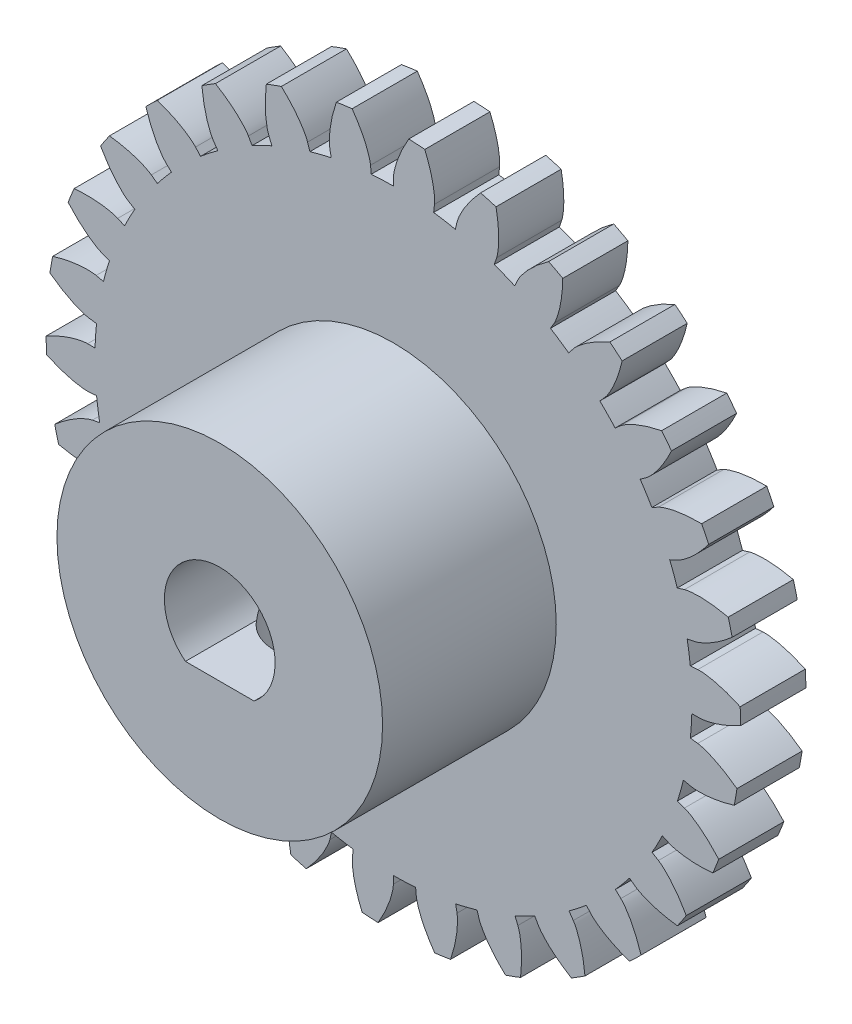
SolidWorks part; units mm, degrees
ref_plane "前视基准面" through (0, 0, 0) normal (0, 0, 1) x (1, 0, 0)
ref_plane "上视基准面" through (0, 0, 0) normal (0, 1, 0) x (1, 0, 0)
ref_plane "右视基准面" through (0, 0, 0) normal (1, 0, 0) x (0, 0, -1)
sketch "草图1" plane through (0, 0, 0) normal (0, 0, 1) x (1, 0, 0)
  line L0 (0, 14.0954) -> (-0.0077, 13.75)
  line L1 (0, 0) -> (0.2236, 14.9983) construction
  line L2 (0, 0) -> (4.2863, 18.7841) construction
  line L3 (0, 0) -> (2.4254, 20.1784) construction
  line L4 (0, 0) -> (1.3782, 20.4589) construction
  line L5 (1.8905, 13.968) -> (1.8518, 13.6247)
  line L6 (0, 0) -> (4.0005, 23.0313) construction
  line L7 (2.9306, 13.7874) -> (2.8513, 13.4511)
  circle A1 centre (0, 0) radius 16
  circle A2 centre (0, 0) radius 13.75
  circle A3 centre (0, 0) radius 15
  spline S0 degree 4 poles (0, 14.0954) (0.0003, 14.1068) (0.0017, 14.1388) (0.0077, 14.1992) (0.0217, 14.2973) (0.046, 14.4215) (0.0846, 14.5806) (0.1395, 14.766) (0.2095, 14.9673) (0.2958, 15.1832) (0.391, 15.3955) (0.4941, 15.6042) (0.6043, 15.809) (0.7462, 16.0534) (0.9281, 16.3408) (1.1575, 16.6679) (1.437, 17.028) (1.7419, 17.3821) (2.058, 17.7198) (2.3951, 18.0476) (2.7339, 18.3552) (3.1028, 18.6598) (3.4522, 18.9336) (3.8613, 19.223) (4.1968, 19.4515) (4.6573, 19.7338) (4.9346, 19.8947) (5.2648, 20.0761) (5.4146, 20.153) (5.5067, 20.2004) knots 0 0 0 0 0 0.005377 0.015084 0.028532 0.04661 0.064855 0.092111 0.119476 0.146842 0.174209 0.201575 0.228941 0.256307 0.307035 0.361767 0.4165 0.471232 0.525964 0.580697 0.635429 0.690161 0.744894 0.799626 0.854358 0.909091 0.954545 1 1 1 1 1 construction
  spline S1 degree 4 poles (0, 14.0954) (0.0003, 14.1068) (0.0017, 14.1388) (0.0077, 14.1992) (0.0217, 14.2973) (0.046, 14.4215) (0.0846, 14.5806) (0.1395, 14.766) (0.2095, 14.9673) (0.2958, 15.1832) (0.391, 15.3955) (0.4941, 15.6042) (0.587, 15.777) (0.6556, 15.8969) (0.6962, 15.9657) (0.7073, 15.9844) knots 0 0 0 0 0 0.005377 0.015084 0.028532 0.04661 0.064855 0.092111 0.119476 0.146842 0.174209 0.201575 0.228941 0.239165 0.239165 0.239165 0.239165 0.239165
  spline S2 degree 4 poles (1.8905, 13.968) (1.8918, 13.9794) (1.8946, 14.0113) (1.8968, 14.072) (1.8961, 14.1711) (1.8887, 14.2973) (1.8717, 14.4602) (1.8422, 14.6513) (1.7999, 14.8602) (1.7432, 15.0857) (1.6774, 15.3088) (1.6032, 15.5295) (1.5343, 15.7131) (1.4825, 15.8412) (1.4515, 15.9148) (1.4429, 15.9348) knots 0 0 0 0 0 0.005377 0.015084 0.028532 0.04661 0.064855 0.092111 0.119476 0.146842 0.174209 0.201575 0.228941 0.239165 0.239165 0.239165 0.239165 0.239165
  spline S3 degree 4 poles (2.9306, 13.7874) (2.9332, 13.7985) (2.9413, 13.8295) (2.9597, 13.8874) (2.9938, 13.9804) (3.0434, 14.0967) (3.1143, 14.2444) (3.2065, 14.4143) (3.3168, 14.5967) (3.4461, 14.7899) (3.5833, 14.9778) (3.7276, 15.1604) (3.8544, 15.3102) (3.9464, 15.4132) (4.0004, 15.4721) (4.0152, 15.488) knots 0 0 0 0 0 0.005377 0.015084 0.028532 0.04661 0.064855 0.092111 0.119476 0.146842 0.174209 0.201575 0.228941 0.239165 0.239165 0.239165 0.239165 0.239165
  dimension "D1" = 30
  dimension "D2" = 32
  dimension "D3" = 27.5
  dimension "D4" = 12
sketch "草图2" plane through (0, 0, 0) normal (0, 0, 1) x (1, 0, 0)
  line L1 (1.8905, 13.968) -> (1.8518, 13.6247) construction
  line L2 (0, 14.0954) -> (-0.0077, 13.75) construction
  line L4 (1.8905, 13.968) -> (1.8518, 13.6247)
  line L5 (0, 14.0954) -> (-0.0077, 13.75)
  line L6 (2.9306, 13.7874) -> (2.8513, 13.4511)
  line L7 (4.7533, 13.2697) -> (4.6441, 12.942)
  line L8 (5.7331, 12.8768) -> (5.5856, 12.5644)
  line L9 (7.4084, 11.9915) -> (7.2334, 11.6936)
  line L10 (8.2851, 11.4034) -> (8.0759, 11.1285)
  line L11 (9.7397, 10.1892) -> (9.5065, 9.9342)
  line L12 (10.4749, 9.4317) -> (10.2131, 9.2062)
  line L13 (11.6453, 7.9415) -> (11.3642, 7.7406)
  line L14 (12.207, 7.0477) -> (11.904, 6.8816)
  line L15 (13.0419, 5.3468) -> (12.7253, 5.2087)
  line L16 (13.4055, 4.3557) -> (13.0747, 4.2563)
  line L17 (13.8686, 2.5184) -> (13.5301, 2.4491)
  line L18 (14.0182, 1.4734) -> (13.6739, 1.4449)
  line L19 (14.0891, -0.4201) -> (13.7437, -0.4175)
  line L20 (14.0182, -1.4734) -> (13.6755, -1.4297)
  line L21 (13.6939, -3.3402) -> (13.3565, -3.2658)
  line L22 (13.4055, -4.3557) -> (13.0794, -4.2417)
  line L23 (12.7002, -6.1143) -> (12.3857, -5.9714)
  line L24 (12.207, -7.0477) -> (11.9117, -6.8684)
  line L25 (11.1514, -8.6212) -> (10.8735, -8.4161)
  line L26 (10.4749, -9.4317) -> (10.2234, -9.1949)
  line L27 (9.1153, -10.7514) -> (8.8861, -10.4929)
  line L28 (8.2851, -11.4034) -> (8.0882, -11.1195)
  line L29 (6.6807, -12.4116) -> (6.5103, -12.1111)
  line L30 (5.7331, -12.8768) -> (5.5996, -12.5581)
  line L31 (3.9542, -13.5294) -> (3.85, -13.2)
  line L32 (2.9306, -13.7874) -> (2.8663, -13.4479)
  line L33 (1.0549, -14.0559) -> (1.0214, -13.712)
  line L34 (0, -14.0954) -> (0.0077, -13.75)
  line L35 (-1.8905, -13.968) -> (-1.8518, -13.6247)
  line L36 (-2.9306, -13.7874) -> (-2.8513, -13.4511)
  line L37 (-4.7533, -13.2697) -> (-4.6441, -12.942)
  line L38 (-5.7331, -12.8768) -> (-5.5856, -12.5644)
  line L39 (-7.4084, -11.9915) -> (-7.2334, -11.6936)
  line L40 (-8.2851, -11.4034) -> (-8.0759, -11.1285)
  line L41 (-9.7397, -10.1892) -> (-9.5065, -9.9342)
  line L42 (-10.4749, -9.4317) -> (-10.2131, -9.2062)
  line L43 (-11.6453, -7.9415) -> (-11.3642, -7.7406)
  line L44 (-12.207, -7.0477) -> (-11.904, -6.8816)
  line L45 (-13.0419, -5.3468) -> (-12.7253, -5.2087)
  line L46 (-13.4055, -4.3557) -> (-13.0747, -4.2563)
  line L47 (-13.8686, -2.5184) -> (-13.5301, -2.4491)
  line L48 (-14.0182, -1.4734) -> (-13.6739, -1.4449)
  line L49 (-14.0891, 0.4201) -> (-13.7437, 0.4175)
  line L50 (-14.0182, 1.4734) -> (-13.6755, 1.4297)
  line L51 (-13.6939, 3.3402) -> (-13.3565, 3.2658)
  line L52 (-13.4055, 4.3557) -> (-13.0794, 4.2417)
  line L53 (-12.7002, 6.1143) -> (-12.3857, 5.9714)
  line L54 (-12.207, 7.0477) -> (-11.9117, 6.8684)
  line L55 (-11.1514, 8.6212) -> (-10.8735, 8.4161)
  line L56 (-10.4749, 9.4317) -> (-10.2234, 9.1949)
  line L57 (-9.1153, 10.7514) -> (-8.8861, 10.4929)
  line L58 (-8.2851, 11.4034) -> (-8.0882, 11.1195)
  line L59 (-6.6807, 12.4116) -> (-6.5103, 12.1111)
  line L60 (-5.7331, 12.8768) -> (-5.5996, 12.5581)
  line L61 (-3.9542, 13.5294) -> (-3.85, 13.2)
  line L62 (-2.9306, 13.7874) -> (-2.8663, 13.4479)
  line L63 (-1.0549, 14.0559) -> (-1.0214, 13.712)
  circle A0 centre (0, 0) radius 13.75 construction
  circle A1 centre (0, 0) radius 16 construction
  arc A2 (2.8513, 13.4511) -> (1.8518, 13.6247) centre (0, 0) ccw
  arc A3 (1.4429, 15.9348) -> (0.7073, 15.9844) centre (0, 0) ccw
  arc A4 (4.7244, 15.2866) -> (4.0152, 15.488) centre (0, 0) ccw
  arc A5 (5.5856, 12.5644) -> (4.6441, 12.942) centre (0, 0) ccw
  arc A6 (7.7995, 13.9703) -> (7.1476, 14.3147) centre (0, 0) ccw
  arc A7 (8.0759, 11.1285) -> (7.2334, 11.6936) centre (0, 0) ccw
  arc A8 (10.5336, 12.0434) -> (9.9676, 12.5159) centre (0, 0) ccw
  arc A9 (10.2131, 9.2062) -> (9.5065, 9.9342) centre (0, 0) ccw
  arc A10 (12.8074, 9.5901) -> (12.352, 10.17) centre (0, 0) ccw
  arc A11 (11.904, 6.8816) -> (11.3642, 7.7406) centre (0, 0) ccw
  arc A12 (14.5214, 6.7178) -> (14.1965, 7.3796) centre (0, 0) ccw
  arc A13 (13.0747, 4.2563) -> (12.7253, 5.2087) centre (0, 0) ccw
  arc A14 (15.6008, 3.5518) -> (15.4206, 4.2667) centre (0, 0) ccw
  arc A15 (13.6739, 1.4449) -> (13.5301, 2.4491) centre (0, 0) ccw
  arc A16 (15.9983, 0.2306) -> (15.9707, 0.9674) centre (0, 0) ccw
  arc A17 (13.6755, -1.4297) -> (13.7437, -0.4175) centre (0, 0) ccw
  arc A18 (15.6967, -3.1007) -> (15.8229, -2.3743) centre (0, 0) ccw
  arc A19 (13.0794, -4.2417) -> (13.3565, -3.2658) centre (0, 0) ccw
  arc A20 (14.709, -6.2964) -> (14.9835, -5.6121) centre (0, 0) ccw
  arc A21 (11.9117, -6.8684) -> (12.3857, -5.9714) centre (0, 0) ccw
  arc A22 (13.0785, -9.217) -> (13.4892, -8.6047) centre (0, 0) ccw
  arc A23 (10.2234, -9.1949) -> (10.8735, -8.4161) centre (0, 0) ccw
  arc A24 (10.8763, -11.7348) -> (11.4054, -11.2213) centre (0, 0) ccw
  arc A25 (8.0882, -11.1195) -> (8.8861, -10.4929) centre (0, 0) ccw
  arc A26 (8.1989, -13.7397) -> (8.8231, -13.3474) centre (0, 0) ccw
  arc A27 (5.5996, -12.5581) -> (6.5103, -12.1111) centre (0, 0) ccw
  arc A28 (5.1631, -15.1441) -> (5.8553, -14.8901) centre (0, 0) ccw
  arc A29 (2.8663, -13.4479) -> (3.85, -13.2) centre (0, 0) ccw
  arc A30 (1.9016, -15.8866) -> (2.6315, -15.7821) centre (0, 0) ccw
  arc A31 (0.0077, -13.75) -> (1.0214, -13.712) centre (0, 0) ccw
  arc A32 (-1.4429, -15.9348) -> (-0.7073, -15.9844) centre (0, 0) ccw
  arc A33 (-2.8513, -13.4511) -> (-1.8518, -13.6247) centre (0, 0) ccw
  arc A34 (-4.7244, -15.2866) -> (-4.0152, -15.488) centre (0, 0) ccw
  arc A35 (-5.5856, -12.5644) -> (-4.6441, -12.942) centre (0, 0) ccw
  arc A36 (-7.7995, -13.9703) -> (-7.1476, -14.3147) centre (0, 0) ccw
  arc A37 (-8.0759, -11.1285) -> (-7.2334, -11.6936) centre (0, 0) ccw
  arc A38 (-10.5336, -12.0434) -> (-9.9676, -12.5159) centre (0, 0) ccw
  arc A39 (-10.2131, -9.2062) -> (-9.5065, -9.9342) centre (0, 0) ccw
  arc A40 (-12.8074, -9.5901) -> (-12.352, -10.17) centre (0, 0) ccw
  arc A41 (-11.904, -6.8816) -> (-11.3642, -7.7406) centre (0, 0) ccw
  arc A42 (-14.5214, -6.7178) -> (-14.1965, -7.3796) centre (0, 0) ccw
  arc A43 (-13.0747, -4.2563) -> (-12.7253, -5.2087) centre (0, 0) ccw
  arc A44 (-15.6008, -3.5518) -> (-15.4206, -4.2667) centre (0, 0) ccw
  arc A45 (-13.6739, -1.4449) -> (-13.5301, -2.4491) centre (0, 0) ccw
  arc A46 (-15.9983, -0.2306) -> (-15.9707, -0.9674) centre (0, 0) ccw
  arc A47 (-13.6755, 1.4297) -> (-13.7437, 0.4175) centre (0, 0) ccw
  arc A48 (-15.6967, 3.1007) -> (-15.8229, 2.3743) centre (0, 0) ccw
  arc A49 (-13.0794, 4.2417) -> (-13.3565, 3.2658) centre (0, 0) ccw
  arc A50 (-14.709, 6.2964) -> (-14.9835, 5.6121) centre (0, 0) ccw
  arc A51 (-11.9117, 6.8684) -> (-12.3857, 5.9714) centre (0, 0) ccw
  arc A52 (-13.0785, 9.217) -> (-13.4892, 8.6047) centre (0, 0) ccw
  arc A53 (-10.2234, 9.1949) -> (-10.8735, 8.4161) centre (0, 0) ccw
  arc A54 (-10.8763, 11.7348) -> (-11.4054, 11.2213) centre (0, 0) ccw
  arc A55 (-8.0882, 11.1195) -> (-8.8861, 10.4929) centre (0, 0) ccw
  arc A56 (-8.1989, 13.7397) -> (-8.8231, 13.3474) centre (0, 0) ccw
  arc A57 (-5.5996, 12.5581) -> (-6.5103, 12.1111) centre (0, 0) ccw
  arc A58 (-5.1631, 15.1441) -> (-5.8553, 14.8901) centre (0, 0) ccw
  arc A59 (-2.8663, 13.4479) -> (-3.85, 13.2) centre (0, 0) ccw
  arc A60 (-1.9016, 15.8866) -> (-2.6315, 15.7821) centre (0, 0) ccw
  arc A61 (-0.0077, 13.75) -> (-1.0214, 13.712) centre (0, 0) ccw
  spline S0 degree 4 poles (2.9306, 13.7874) (2.9332, 13.7985) (2.9413, 13.8295) (2.9597, 13.8874) (2.9938, 13.9804) (3.0434, 14.0967) (3.1143, 14.2444) (3.2065, 14.4143) (3.3168, 14.5967) (3.4461, 14.7899) (3.5833, 14.9778) (3.7276, 15.1604) (3.8544, 15.3102) (3.9464, 15.4132) (4.0004, 15.4721) (4.0152, 15.488) knots 0 0 0 0 0 0.005377 0.015084 0.028532 0.04661 0.064855 0.092111 0.119476 0.146842 0.174209 0.201575 0.228941 0.239165 0.239165 0.239165 0.239165 0.239165
  spline S1 degree 4 poles (-1981.9563, 266.1044) (-29.2898, 14.94) (1.0975, 12.0268) (1.9043, 13.0778) (1.8961, 14.1711) (1.8887, 14.2973) (1.8717, 14.4602) (1.8422, 14.6513) (1.7999, 14.8602) (1.7432, 15.0857) (1.6774, 15.3088) (1.6032, 15.5295) (-0.0416, 19.9172) (-5.4948, 22.8946) (6.4922, 14.9969) (-1610.7354, 1199.459) knots -0.467666 -0.467666 -0.467666 -0.467666 -0.467666 0.005377 0.015084 0.028532 0.04661 0.064855 0.092111 0.119476 0.146842 0.174209 0.201575 0.228941 2.352251 2.352251 2.352251 2.352251 2.352251 only from (1.8905, 13.968) to (1.4429, 15.9348) construction
  spline S2 degree 4 poles (1999.7394, -2.1255) (31.029, 10.8766) (0.5255, 12.0653) (-0.1331, 13.2151) (0.0217, 14.2973) (0.046, 14.4215) (0.0846, 14.5806) (0.1395, 14.766) (0.2095, 14.9673) (0.2958, 15.1832) (0.391, 15.3955) (0.4941, 15.6042) (2.7126, 19.7317) (8.5158, 21.9507) (-4.4221, 15.7322) (1757.0568, 972.5852) knots -0.467666 -0.467666 -0.467666 -0.467666 -0.467666 0.005377 0.015084 0.028532 0.04661 0.064855 0.092111 0.119476 0.146842 0.174209 0.201575 0.228941 2.352251 2.352251 2.352251 2.352251 2.352251 only from (0, 14.0954) to (0.7073, 15.9844) construction
  spline S3 degree 4 poles (4.7533, 13.2697) (4.7569, 13.2806) (4.7663, 13.3112) (4.7811, 13.3701) (4.801, 13.4672) (4.82, 13.5922) (4.8372, 13.755) (4.8481, 13.9481) (4.8502, 14.1612) (4.8416, 14.3936) (4.8237, 14.6255) (4.7969, 14.8568) (4.7678, 15.0508) (4.7437, 15.1868) (4.7286, 15.2653) (4.7244, 15.2866) knots 0 0 0 0 0 0.005377 0.015084 0.028532 0.04661 0.064855 0.092111 0.119476 0.146842 0.174209 0.201575 0.228941 0.239165 0.239165 0.239165 0.239165 0.239165
  spline S4 degree 4 poles (1.8905, 13.968) (1.8918, 13.9794) (1.8946, 14.0113) (1.8968, 14.072) (1.8961, 14.1711) (1.8887, 14.2973) (1.8717, 14.4602) (1.8422, 14.6513) (1.7999, 14.8602) (1.7432, 15.0857) (1.6774, 15.3088) (1.6032, 15.5295) (1.5343, 15.7131) (1.4825, 15.8412) (1.4515, 15.9148) (1.4429, 15.9348) knots 0 0 0 0 0 0.005377 0.015084 0.028532 0.04661 0.064855 0.092111 0.119476 0.146842 0.174209 0.201575 0.228941 0.239165 0.239165 0.239165 0.239165 0.239165
  spline S5 degree 4 poles (0, 14.0954) (0.0003, 14.1068) (0.0017, 14.1388) (0.0077, 14.1992) (0.0217, 14.2973) (0.046, 14.4215) (0.0846, 14.5806) (0.1395, 14.766) (0.2095, 14.9673) (0.2958, 15.1832) (0.391, 15.3955) (0.4941, 15.6042) (0.587, 15.777) (0.6556, 15.8969) (0.6962, 15.9657) (0.7073, 15.9844) knots 0 0 0 0 0 0.005377 0.015084 0.028532 0.04661 0.064855 0.092111 0.119476 0.146842 0.174209 0.201575 0.228941 0.239165 0.239165 0.239165 0.239165 0.239165
  spline S6 degree 4 poles (5.7331, 12.8768) (5.738, 12.8871) (5.7524, 12.9158) (5.7824, 12.9685) (5.8351, 13.0524) (5.9077, 13.156) (6.0078, 13.2856) (6.1333, 13.4327) (6.2791, 13.5881) (6.4458, 13.7502) (6.6191, 13.9055) (6.7982, 14.0541) (6.9533, 14.1742) (7.0647, 14.2559) (7.1298, 14.3022) (7.1476, 14.3147) knots 0 0 0 0 0 0.005377 0.015084 0.028532 0.04661 0.064855 0.092111 0.119476 0.146842 0.174209 0.201575 0.228941 0.239165 0.239165 0.239165 0.239165 0.239165
  spline S7 degree 4 poles (7.4084, 11.9915) (7.4142, 12.0013) (7.4297, 12.0294) (7.4564, 12.0839) (7.4961, 12.1747) (7.5406, 12.293) (7.5914, 12.4487) (7.6422, 12.6353) (7.6884, 12.8433) (7.7284, 13.0724) (7.7591, 13.303) (7.781, 13.5348) (7.7928, 13.7306) (7.7975, 13.8686) (7.7991, 13.9485) (7.7995, 13.9703) knots 0 0 0 0 0 0.005377 0.015084 0.028532 0.04661 0.064855 0.092111 0.119476 0.146842 0.174209 0.201575 0.228941 0.239165 0.239165 0.239165 0.239165 0.239165
  spline S8 degree 4 poles (8.2851, 11.4034) (8.292, 11.4125) (8.312, 11.4375) (8.3523, 11.4829) (8.4213, 11.554) (8.5139, 11.6402) (8.6387, 11.7462) (8.7921, 11.8639) (8.967, 11.9857) (9.1638, 12.1096) (9.3656, 12.2254) (9.5717, 12.3336) (9.7484, 12.4188) (9.8743, 12.4755) (9.9476, 12.5073) (9.9676, 12.5159) knots 0 0 0 0 0 0.005377 0.015084 0.028532 0.04661 0.064855 0.092111 0.119476 0.146842 0.174209 0.201575 0.228941 0.239165 0.239165 0.239165 0.239165 0.239165
  spline S9 degree 4 poles (9.7397, 10.1892) (9.7474, 10.1976) (9.7684, 10.2218) (9.8059, 10.2695) (9.8635, 10.3501) (9.9317, 10.4566) (10.0137, 10.5984) (10.1022, 10.7703) (10.1907, 10.9642) (10.2775, 11.1799) (10.3554, 11.3991) (10.425, 11.6213) (10.4773, 11.8103) (10.5106, 11.9444) (10.5287, 12.0222) (10.5336, 12.0434) knots 0 0 0 0 0 0.005377 0.015084 0.028532 0.04661 0.064855 0.092111 0.119476 0.146842 0.174209 0.201575 0.228941 0.239165 0.239165 0.239165 0.239165 0.239165
  spline S10 degree 4 poles (10.4749, 9.4317) (10.4836, 9.4391) (10.5084, 9.4594) (10.5572, 9.4954) (10.6395, 9.5507) (10.748, 9.6157) (10.8921, 9.6934) (11.0666, 9.7767) (11.263, 9.8594) (11.4813, 9.9397) (11.7027, 10.011) (11.9268, 10.074) (12.1174, 10.1206) (12.2523, 10.1499) (12.3307, 10.1658) (12.352, 10.17) knots 0 0 0 0 0 0.005377 0.015084 0.028532 0.04661 0.064855 0.092111 0.119476 0.146842 0.174209 0.201575 0.228941 0.239165 0.239165 0.239165 0.239165 0.239165
  spline S11 degree 4 poles (11.6453, 7.9415) (11.6546, 7.9482) (11.6802, 7.9674) (11.7267, 8.0064) (11.7999, 8.0732) (11.8888, 8.1632) (11.9984, 8.2848) (12.1207, 8.4346) (12.2476, 8.6058) (12.3773, 8.7988) (12.4991, 8.997) (12.6134, 9.1998) (12.7038, 9.3739) (12.7643, 9.4981) (12.7982, 9.5704) (12.8074, 9.5901) knots 0 0 0 0 0 0.005377 0.015084 0.028532 0.04661 0.064855 0.092111 0.119476 0.146842 0.174209 0.201575 0.228941 0.239165 0.239165 0.239165 0.239165 0.239165
  spline S12 degree 4 poles (12.207, 7.0477) (12.217, 7.0532) (12.2455, 7.0679) (12.3007, 7.093) (12.3927, 7.1299) (12.5123, 7.1709) (12.6695, 7.217) (12.8575, 7.2622) (13.0668, 7.3022) (13.2969, 7.3354) (13.5284, 7.3591) (13.7607, 7.3741) (13.9568, 7.3801) (14.0949, 7.3807) (14.1748, 7.3799) (14.1965, 7.3796) knots 0 0 0 0 0 0.005377 0.015084 0.028532 0.04661 0.064855 0.092111 0.119476 0.146842 0.174209 0.201575 0.228941 0.239165 0.239165 0.239165 0.239165 0.239165
  spline S13 degree 4 poles (13.0419, 5.3468) (13.0524, 5.3514) (13.0815, 5.3649) (13.1351, 5.3933) (13.2205, 5.4435) (13.3262, 5.513) (13.4587, 5.6091) (13.6095, 5.7303) (13.7692, 5.8713) (13.9362, 6.0331) (14.0966, 6.2017) (14.2505, 6.3763) (14.3752, 6.5278) (14.4601, 6.6367) (14.5084, 6.7004) (14.5214, 6.7178) knots 0 0 0 0 0 0.005377 0.015084 0.028532 0.04661 0.064855 0.092111 0.119476 0.146842 0.174209 0.201575 0.228941 0.239165 0.239165 0.239165 0.239165 0.239165
  spline S14 degree 4 poles (13.4055, 4.3557) (13.4165, 4.359) (13.4474, 4.3675) (13.5066, 4.3805) (13.6043, 4.3975) (13.7298, 4.4128) (13.8931, 4.4251) (14.0864, 4.4303) (14.2995, 4.4259) (14.5315, 4.4105) (14.7628, 4.3856) (14.9932, 4.352) (15.1862, 4.3171) (15.3214, 4.2889) (15.3994, 4.2715) (15.4206, 4.2667) knots 0 0 0 0 0 0.005377 0.015084 0.028532 0.04661 0.064855 0.092111 0.119476 0.146842 0.174209 0.201575 0.228941 0.239165 0.239165 0.239165 0.239165 0.239165
  spline S15 degree 4 poles (13.8686, 2.5184) (13.8798, 2.5207) (13.911, 2.5279) (13.9694, 2.5445) (14.0634, 2.5758) (14.1812, 2.6219) (14.3308, 2.6883) (14.5035, 2.7755) (14.689, 2.8802) (14.886, 3.0038) (15.0779, 3.1354) (15.2648, 3.2741) (15.4182, 3.3964) (15.524, 3.4853) (15.5844, 3.5375) (15.6008, 3.5518) knots 0 0 0 0 0 0.005377 0.015084 0.028532 0.04661 0.064855 0.092111 0.119476 0.146842 0.174209 0.201575 0.228941 0.239165 0.239165 0.239165 0.239165 0.239165
  spline S16 degree 4 poles (14.0182, 1.4734) (14.0296, 1.4743) (14.0616, 1.4762) (14.1222, 1.4766) (14.2213, 1.4729) (14.3473, 1.4617) (14.5095, 1.4399) (14.6997, 1.4047) (14.9072, 1.3562) (15.1309, 1.2929) (15.352, 1.2204) (15.5703, 1.1396) (15.7519, 1.0653) (15.8783, 1.0097) (15.951, 0.9765) (15.9707, 0.9674) knots 0 0 0 0 0 0.005377 0.015084 0.028532 0.04661 0.064855 0.092111 0.119476 0.146842 0.174209 0.201575 0.228941 0.239165 0.239165 0.239165 0.239165 0.239165
  spline S17 degree 4 poles (14.0891, -0.4201) (14.1006, -0.4202) (14.1326, -0.4196) (14.1932, -0.4155) (14.2916, -0.4044) (14.4164, -0.3839) (14.5766, -0.3499) (14.7636, -0.3006) (14.9669, -0.2367) (15.1853, -0.1568) (15.4003, -0.068) (15.612, 0.0289) (15.7874, 0.1165) (15.9094, 0.1815) (15.9793, 0.22) (15.9983, 0.2306) knots 0 0 0 0 0 0.005377 0.015084 0.028532 0.04661 0.064855 0.092111 0.119476 0.146842 0.174209 0.201575 0.228941 0.239165 0.239165 0.239165 0.239165 0.239165
  spline S18 degree 4 poles (14.0182, -1.4734) (14.0295, -1.4748) (14.0612, -1.4796) (14.1206, -1.4918) (14.2167, -1.5161) (14.3376, -1.5532) (14.4918, -1.6083) (14.6705, -1.6822) (14.8634, -1.7728) (15.0691, -1.8813) (15.2703, -1.9981) (15.467, -2.1225) (15.6292, -2.2329) (15.7413, -2.3136) (15.8055, -2.3612) (15.8229, -2.3743) knots 0 0 0 0 0 0.005377 0.015084 0.028532 0.04661 0.064855 0.092111 0.119476 0.146842 0.174209 0.201575 0.228941 0.239165 0.239165 0.239165 0.239165 0.239165
  spline S19 degree 4 poles (13.6939, -3.3402) (13.7051, -3.3427) (13.7365, -3.3488) (13.7966, -3.3574) (13.8952, -3.367) (14.0216, -3.3728) (14.1853, -3.373) (14.3785, -3.3636) (14.5906, -3.3433) (14.8208, -3.3106) (15.0496, -3.2685) (15.2768, -3.2177) (15.4667, -3.1684) (15.5994, -3.1302) (15.6759, -3.1071) (15.6967, -3.1007) knots 0 0 0 0 0 0.005377 0.015084 0.028532 0.04661 0.064855 0.092111 0.119476 0.146842 0.174209 0.201575 0.228941 0.239165 0.239165 0.239165 0.239165 0.239165
  spline S20 degree 4 poles (13.4055, -4.3557) (13.4163, -4.3595) (13.4463, -4.3708) (13.5019, -4.3951) (13.5909, -4.4387) (13.7014, -4.5002) (13.8408, -4.5861) (14.0002, -4.6956) (14.17, -4.8244) (14.3486, -4.9732) (14.5212, -5.1293) (14.6878, -5.2919) (14.8234, -5.4336) (14.9163, -5.5359) (14.9691, -5.5958) (14.9835, -5.6121) knots 0 0 0 0 0 0.005377 0.015084 0.028532 0.04661 0.064855 0.092111 0.119476 0.146842 0.174209 0.201575 0.228941 0.239165 0.239165 0.239165 0.239165 0.239165
  spline S21 degree 4 poles (12.7002, -6.1143) (12.7106, -6.1191) (12.7401, -6.1316) (12.7971, -6.1525) (12.8915, -6.1824) (13.0139, -6.2144) (13.1741, -6.2485) (13.3649, -6.2795) (13.5767, -6.3038) (13.8086, -6.3197) (14.0412, -6.326) (14.274, -6.3236) (14.4699, -6.3149) (14.6077, -6.3051) (14.6874, -6.2984) (14.709, -6.2964) knots 0 0 0 0 0 0.005377 0.015084 0.028532 0.04661 0.064855 0.092111 0.119476 0.146842 0.174209 0.201575 0.228941 0.239165 0.239165 0.239165 0.239165 0.239165
  spline S22 degree 4 poles (12.207, -7.0477) (12.2167, -7.0536) (12.2437, -7.0709) (12.2931, -7.1063) (12.371, -7.1674) (12.4664, -7.2505) (12.5848, -7.3636) (12.718, -7.5038) (12.8573, -7.665) (13.0011, -7.8478) (13.1374, -8.0364) (13.2665, -8.23) (13.3697, -8.3968) (13.4393, -8.5162) (13.4786, -8.5858) (13.4892, -8.6047) knots 0 0 0 0 0 0.005377 0.015084 0.028532 0.04661 0.064855 0.092111 0.119476 0.146842 0.174209 0.201575 0.228941 0.239165 0.239165 0.239165 0.239165 0.239165
  spline S23 degree 4 poles (11.1514, -8.6212) (11.1606, -8.628) (11.1869, -8.6464) (11.2383, -8.6787) (11.3244, -8.7276) (11.4375, -8.7843) (11.587, -8.851) (11.7673, -8.921) (11.9693, -8.9888) (12.193, -9.0525) (12.4191, -9.1071) (12.6473, -9.1531) (12.8408, -9.1854) (12.9776, -9.2045) (13.0569, -9.2144) (13.0785, -9.217) knots 0 0 0 0 0 0.005377 0.015084 0.028532 0.04661 0.064855 0.092111 0.119476 0.146842 0.174209 0.201575 0.228941 0.239165 0.239165 0.239165 0.239165 0.239165
  spline S24 degree 4 poles (10.4749, -9.4317) (10.4832, -9.4395) (10.506, -9.462) (10.547, -9.5068) (10.6105, -9.5829) (10.6865, -9.684) (10.7788, -9.8192) (10.8799, -9.9841) (10.9827, -10.1707) (11.0854, -10.3794) (11.1795, -10.5922) (11.2655, -10.8084) (11.3318, -10.9931) (11.375, -11.1243) (11.399, -11.2005) (11.4054, -11.2213) knots 0 0 0 0 0 0.005377 0.015084 0.028532 0.04661 0.064855 0.092111 0.119476 0.146842 0.174209 0.201575 0.228941 0.239165 0.239165 0.239165 0.239165 0.239165
  spline S25 degree 4 poles (9.1153, -10.7514) (9.1229, -10.7599) (9.1447, -10.7834) (9.1883, -10.8256) (9.2624, -10.8914) (9.3612, -10.9703) (9.4936, -11.0667) (9.6554, -11.1727) (9.8389, -11.281) (10.0444, -11.3898) (10.2543, -11.4902) (10.4679, -11.5826) (10.6505, -11.6544) (10.7803, -11.7015) (10.8558, -11.7277) (10.8763, -11.7348) knots 0 0 0 0 0 0.005377 0.015084 0.028532 0.04661 0.064855 0.092111 0.119476 0.146842 0.174209 0.201575 0.228941 0.239165 0.239165 0.239165 0.239165 0.239165
  spline S26 degree 4 poles (8.2851, -11.4034) (8.2916, -11.4128) (8.3092, -11.4396) (8.3399, -11.4919) (8.3862, -11.5795) (8.4395, -11.6942) (8.5018, -11.8457) (8.5664, -12.028) (8.6281, -12.2319) (8.6851, -12.4573) (8.7329, -12.685) (8.7721, -12.9145) (8.7986, -13.1089) (8.8136, -13.2462) (8.8212, -13.3257) (8.8231, -13.3474) knots 0 0 0 0 0 0.005377 0.015084 0.028532 0.04661 0.064855 0.092111 0.119476 0.146842 0.174209 0.201575 0.228941 0.239165 0.239165 0.239165 0.239165 0.239165
  spline S27 degree 4 poles (6.6807, -12.4116) (6.6864, -12.4215) (6.7029, -12.449) (6.7367, -12.4994) (6.7956, -12.5791) (6.8758, -12.6769) (6.9852, -12.7987) (7.1214, -12.936) (7.2784, -13.0801) (7.4568, -13.2292) (7.6412, -13.3711) (7.831, -13.5059) (7.9946, -13.6141) (8.1118, -13.6872) (8.1802, -13.7285) (8.1989, -13.7397) knots 0 0 0 0 0 0.005377 0.015084 0.028532 0.04661 0.064855 0.092111 0.119476 0.146842 0.174209 0.201575 0.228941 0.239165 0.239165 0.239165 0.239165 0.239165
  spline S28 degree 4 poles (5.7331, -12.8768) (5.7375, -12.8873) (5.7492, -12.9172) (5.7683, -12.9748) (5.7954, -13.0701) (5.8237, -13.1933) (5.8531, -13.3544) (5.8784, -13.5462) (5.8964, -13.7585) (5.9053, -13.9909) (5.9047, -14.2235) (5.8954, -14.4561) (5.8808, -14.6517) (5.867, -14.7892) (5.8578, -14.8685) (5.8553, -14.8901) knots 0 0 0 0 0 0.005377 0.015084 0.028532 0.04661 0.064855 0.092111 0.119476 0.146842 0.174209 0.201575 0.228941 0.239165 0.239165 0.239165 0.239165 0.239165
  spline S29 degree 4 poles (3.9542, -13.5294) (3.9577, -13.5403) (3.9681, -13.5706) (3.9907, -13.6269) (4.0317, -13.7171) (4.0898, -13.8294) (4.1716, -13.9713) (4.2763, -14.1339) (4.3999, -14.3075) (4.5434, -14.4905) (4.6943, -14.6676) (4.8518, -14.839) (4.9894, -14.9787) (5.0889, -15.0746) (5.1472, -15.1293) (5.1631, -15.1441) knots 0 0 0 0 0 0.005377 0.015084 0.028532 0.04661 0.064855 0.092111 0.119476 0.146842 0.174209 0.201575 0.228941 0.239165 0.239165 0.239165 0.239165 0.239165
  spline S30 degree 4 poles (2.9306, -13.7874) (2.9327, -13.7986) (2.9379, -13.8302) (2.9447, -13.8905) (2.9514, -13.9894) (2.9534, -14.1159) (2.9487, -14.2795) (2.9336, -14.4723) (2.907, -14.6838) (2.8674, -14.9129) (2.8185, -15.1404) (2.7609, -15.3659) (2.706, -15.5542) (2.6639, -15.6858) (2.6385, -15.7615) (2.6315, -15.7821) knots 0 0 0 0 0 0.005377 0.015084 0.028532 0.04661 0.064855 0.092111 0.119476 0.146842 0.174209 0.201575 0.228941 0.239165 0.239165 0.239165 0.239165 0.239165
  spline S31 degree 4 poles (1.0549, -14.0559) (1.056, -14.0672) (1.0599, -14.0991) (1.0703, -14.1588) (1.0917, -14.2556) (1.1252, -14.3776) (1.1756, -14.5333) (1.2442, -14.7142) (1.329, -14.9096) (1.4313, -15.1185) (1.5421, -15.3231) (1.6606, -15.5234) (1.7661, -15.6888) (1.8435, -15.8032) (1.8891, -15.8688) (1.9016, -15.8866) knots 0 0 0 0 0 0.005377 0.015084 0.028532 0.04661 0.064855 0.092111 0.119476 0.146842 0.174209 0.201575 0.228941 0.239165 0.239165 0.239165 0.239165 0.239165
  spline S32 degree 4 poles (0, -14.0954) (-0.0003, -14.1068) (-0.0017, -14.1388) (-0.0077, -14.1992) (-0.0217, -14.2973) (-0.046, -14.4215) (-0.0846, -14.5806) (-0.1395, -14.766) (-0.2095, -14.9673) (-0.2958, -15.1832) (-0.391, -15.3955) (-0.4941, -15.6042) (-0.587, -15.777) (-0.6556, -15.8969) (-0.6962, -15.9657) (-0.7073, -15.9844) knots 0 0 0 0 0 0.005377 0.015084 0.028532 0.04661 0.064855 0.092111 0.119476 0.146842 0.174209 0.201575 0.228941 0.239165 0.239165 0.239165 0.239165 0.239165
  spline S33 degree 4 poles (-1.8905, -13.968) (-1.8918, -13.9794) (-1.8946, -14.0113) (-1.8968, -14.072) (-1.8961, -14.1711) (-1.8887, -14.2973) (-1.8717, -14.4602) (-1.8422, -14.6513) (-1.7999, -14.8602) (-1.7432, -15.0857) (-1.6774, -15.3088) (-1.6032, -15.5295) (-1.5343, -15.7131) (-1.4825, -15.8412) (-1.4515, -15.9148) (-1.4429, -15.9348) knots 0 0 0 0 0 0.005377 0.015084 0.028532 0.04661 0.064855 0.092111 0.119476 0.146842 0.174209 0.201575 0.228941 0.239165 0.239165 0.239165 0.239165 0.239165
  spline S34 degree 4 poles (-2.9306, -13.7874) (-2.9332, -13.7985) (-2.9413, -13.8295) (-2.9597, -13.8874) (-2.9938, -13.9804) (-3.0434, -14.0967) (-3.1143, -14.2444) (-3.2065, -14.4143) (-3.3168, -14.5967) (-3.4461, -14.7899) (-3.5833, -14.9778) (-3.7276, -15.1604) (-3.8544, -15.3102) (-3.9464, -15.4132) (-4.0004, -15.4721) (-4.0152, -15.488) knots 0 0 0 0 0 0.005377 0.015084 0.028532 0.04661 0.064855 0.092111 0.119476 0.146842 0.174209 0.201575 0.228941 0.239165 0.239165 0.239165 0.239165 0.239165
  spline S35 degree 4 poles (-4.7533, -13.2697) (-4.7569, -13.2806) (-4.7663, -13.3112) (-4.7811, -13.3701) (-4.801, -13.4672) (-4.82, -13.5922) (-4.8372, -13.755) (-4.8481, -13.9481) (-4.8502, -14.1612) (-4.8416, -14.3936) (-4.8237, -14.6255) (-4.7969, -14.8568) (-4.7678, -15.0508) (-4.7437, -15.1868) (-4.7286, -15.2653) (-4.7244, -15.2866) knots 0 0 0 0 0 0.005377 0.015084 0.028532 0.04661 0.064855 0.092111 0.119476 0.146842 0.174209 0.201575 0.228941 0.239165 0.239165 0.239165 0.239165 0.239165
  spline S36 degree 4 poles (-5.7331, -12.8768) (-5.738, -12.8871) (-5.7524, -12.9158) (-5.7824, -12.9685) (-5.8351, -13.0524) (-5.9077, -13.156) (-6.0078, -13.2856) (-6.1333, -13.4327) (-6.2791, -13.5881) (-6.4458, -13.7502) (-6.6191, -13.9055) (-6.7982, -14.0541) (-6.9533, -14.1742) (-7.0647, -14.2559) (-7.1298, -14.3022) (-7.1476, -14.3147) knots 0 0 0 0 0 0.005377 0.015084 0.028532 0.04661 0.064855 0.092111 0.119476 0.146842 0.174209 0.201575 0.228941 0.239165 0.239165 0.239165 0.239165 0.239165
  spline S37 degree 4 poles (-7.4084, -11.9915) (-7.4142, -12.0013) (-7.4297, -12.0294) (-7.4564, -12.0839) (-7.4961, -12.1747) (-7.5406, -12.293) (-7.5914, -12.4487) (-7.6422, -12.6353) (-7.6884, -12.8433) (-7.7284, -13.0724) (-7.7591, -13.303) (-7.781, -13.5348) (-7.7928, -13.7306) (-7.7975, -13.8686) (-7.7991, -13.9485) (-7.7995, -13.9703) knots 0 0 0 0 0 0.005377 0.015084 0.028532 0.04661 0.064855 0.092111 0.119476 0.146842 0.174209 0.201575 0.228941 0.239165 0.239165 0.239165 0.239165 0.239165
  spline S38 degree 4 poles (-8.2851, -11.4034) (-8.292, -11.4125) (-8.312, -11.4375) (-8.3523, -11.4829) (-8.4213, -11.554) (-8.5139, -11.6402) (-8.6387, -11.7462) (-8.7921, -11.8639) (-8.967, -11.9857) (-9.1638, -12.1096) (-9.3656, -12.2254) (-9.5717, -12.3336) (-9.7484, -12.4188) (-9.8743, -12.4755) (-9.9476, -12.5073) (-9.9676, -12.5159) knots 0 0 0 0 0 0.005377 0.015084 0.028532 0.04661 0.064855 0.092111 0.119476 0.146842 0.174209 0.201575 0.228941 0.239165 0.239165 0.239165 0.239165 0.239165
  spline S39 degree 4 poles (-9.7397, -10.1892) (-9.7474, -10.1976) (-9.7684, -10.2218) (-9.8059, -10.2695) (-9.8635, -10.3501) (-9.9317, -10.4566) (-10.0137, -10.5984) (-10.1022, -10.7703) (-10.1907, -10.9642) (-10.2775, -11.1799) (-10.3554, -11.3991) (-10.425, -11.6213) (-10.4773, -11.8103) (-10.5106, -11.9444) (-10.5287, -12.0222) (-10.5336, -12.0434) knots 0 0 0 0 0 0.005377 0.015084 0.028532 0.04661 0.064855 0.092111 0.119476 0.146842 0.174209 0.201575 0.228941 0.239165 0.239165 0.239165 0.239165 0.239165
  spline S40 degree 4 poles (-10.4749, -9.4317) (-10.4836, -9.4391) (-10.5084, -9.4594) (-10.5572, -9.4954) (-10.6395, -9.5507) (-10.748, -9.6157) (-10.8921, -9.6934) (-11.0666, -9.7767) (-11.263, -9.8594) (-11.4813, -9.9397) (-11.7027, -10.011) (-11.9268, -10.074) (-12.1174, -10.1206) (-12.2523, -10.1499) (-12.3307, -10.1658) (-12.352, -10.17) knots 0 0 0 0 0 0.005377 0.015084 0.028532 0.04661 0.064855 0.092111 0.119476 0.146842 0.174209 0.201575 0.228941 0.239165 0.239165 0.239165 0.239165 0.239165
  spline S41 degree 4 poles (-11.6453, -7.9415) (-11.6546, -7.9482) (-11.6802, -7.9674) (-11.7267, -8.0064) (-11.7999, -8.0732) (-11.8888, -8.1632) (-11.9984, -8.2848) (-12.1207, -8.4346) (-12.2476, -8.6058) (-12.3773, -8.7988) (-12.4991, -8.997) (-12.6134, -9.1998) (-12.7038, -9.3739) (-12.7643, -9.4981) (-12.7982, -9.5704) (-12.8074, -9.5901) knots 0 0 0 0 0 0.005377 0.015084 0.028532 0.04661 0.064855 0.092111 0.119476 0.146842 0.174209 0.201575 0.228941 0.239165 0.239165 0.239165 0.239165 0.239165
  spline S42 degree 4 poles (-12.207, -7.0477) (-12.217, -7.0532) (-12.2455, -7.0679) (-12.3007, -7.093) (-12.3927, -7.1299) (-12.5123, -7.1709) (-12.6695, -7.217) (-12.8575, -7.2622) (-13.0668, -7.3022) (-13.2969, -7.3354) (-13.5284, -7.3591) (-13.7607, -7.3741) (-13.9568, -7.3801) (-14.0949, -7.3807) (-14.1748, -7.3799) (-14.1965, -7.3796) knots 0 0 0 0 0 0.005377 0.015084 0.028532 0.04661 0.064855 0.092111 0.119476 0.146842 0.174209 0.201575 0.228941 0.239165 0.239165 0.239165 0.239165 0.239165
  spline S43 degree 4 poles (-13.0419, -5.3468) (-13.0524, -5.3514) (-13.0815, -5.3649) (-13.1351, -5.3933) (-13.2205, -5.4435) (-13.3262, -5.513) (-13.4587, -5.6091) (-13.6095, -5.7303) (-13.7692, -5.8713) (-13.9362, -6.0331) (-14.0966, -6.2017) (-14.2505, -6.3763) (-14.3752, -6.5278) (-14.4601, -6.6367) (-14.5084, -6.7004) (-14.5214, -6.7178) knots 0 0 0 0 0 0.005377 0.015084 0.028532 0.04661 0.064855 0.092111 0.119476 0.146842 0.174209 0.201575 0.228941 0.239165 0.239165 0.239165 0.239165 0.239165
  spline S44 degree 4 poles (-13.4055, -4.3557) (-13.4165, -4.359) (-13.4474, -4.3675) (-13.5066, -4.3805) (-13.6043, -4.3975) (-13.7298, -4.4128) (-13.8931, -4.4251) (-14.0864, -4.4303) (-14.2995, -4.4259) (-14.5315, -4.4105) (-14.7628, -4.3856) (-14.9932, -4.352) (-15.1862, -4.3171) (-15.3214, -4.2889) (-15.3994, -4.2715) (-15.4206, -4.2667) knots 0 0 0 0 0 0.005377 0.015084 0.028532 0.04661 0.064855 0.092111 0.119476 0.146842 0.174209 0.201575 0.228941 0.239165 0.239165 0.239165 0.239165 0.239165
  spline S45 degree 4 poles (-13.8686, -2.5184) (-13.8798, -2.5207) (-13.911, -2.5279) (-13.9694, -2.5445) (-14.0634, -2.5758) (-14.1812, -2.6219) (-14.3308, -2.6883) (-14.5035, -2.7755) (-14.689, -2.8802) (-14.886, -3.0038) (-15.0779, -3.1354) (-15.2648, -3.2741) (-15.4182, -3.3964) (-15.524, -3.4853) (-15.5844, -3.5375) (-15.6008, -3.5518) knots 0 0 0 0 0 0.005377 0.015084 0.028532 0.04661 0.064855 0.092111 0.119476 0.146842 0.174209 0.201575 0.228941 0.239165 0.239165 0.239165 0.239165 0.239165
  spline S46 degree 4 poles (-14.0182, -1.4734) (-14.0296, -1.4743) (-14.0616, -1.4762) (-14.1222, -1.4766) (-14.2213, -1.4729) (-14.3473, -1.4617) (-14.5095, -1.4399) (-14.6997, -1.4047) (-14.9072, -1.3562) (-15.1309, -1.2929) (-15.352, -1.2204) (-15.5703, -1.1396) (-15.7519, -1.0653) (-15.8783, -1.0097) (-15.951, -0.9765) (-15.9707, -0.9674) knots 0 0 0 0 0 0.005377 0.015084 0.028532 0.04661 0.064855 0.092111 0.119476 0.146842 0.174209 0.201575 0.228941 0.239165 0.239165 0.239165 0.239165 0.239165
  spline S47 degree 4 poles (-14.0891, 0.4201) (-14.1006, 0.4202) (-14.1326, 0.4196) (-14.1932, 0.4155) (-14.2916, 0.4044) (-14.4164, 0.3839) (-14.5766, 0.3499) (-14.7636, 0.3006) (-14.9669, 0.2367) (-15.1853, 0.1568) (-15.4003, 0.068) (-15.612, -0.0289) (-15.7874, -0.1165) (-15.9094, -0.1815) (-15.9793, -0.22) (-15.9983, -0.2306) knots 0 0 0 0 0 0.005377 0.015084 0.028532 0.04661 0.064855 0.092111 0.119476 0.146842 0.174209 0.201575 0.228941 0.239165 0.239165 0.239165 0.239165 0.239165
  spline S48 degree 4 poles (-14.0182, 1.4734) (-14.0295, 1.4748) (-14.0612, 1.4796) (-14.1206, 1.4918) (-14.2167, 1.5161) (-14.3376, 1.5532) (-14.4918, 1.6083) (-14.6705, 1.6822) (-14.8634, 1.7728) (-15.0691, 1.8813) (-15.2703, 1.9981) (-15.467, 2.1225) (-15.6292, 2.2329) (-15.7413, 2.3136) (-15.8055, 2.3612) (-15.8229, 2.3743) knots 0 0 0 0 0 0.005377 0.015084 0.028532 0.04661 0.064855 0.092111 0.119476 0.146842 0.174209 0.201575 0.228941 0.239165 0.239165 0.239165 0.239165 0.239165
  spline S49 degree 4 poles (-13.6939, 3.3402) (-13.7051, 3.3427) (-13.7365, 3.3488) (-13.7966, 3.3574) (-13.8952, 3.367) (-14.0216, 3.3728) (-14.1853, 3.373) (-14.3785, 3.3636) (-14.5906, 3.3433) (-14.8208, 3.3106) (-15.0496, 3.2685) (-15.2768, 3.2177) (-15.4667, 3.1684) (-15.5994, 3.1302) (-15.6759, 3.1071) (-15.6967, 3.1007) knots 0 0 0 0 0 0.005377 0.015084 0.028532 0.04661 0.064855 0.092111 0.119476 0.146842 0.174209 0.201575 0.228941 0.239165 0.239165 0.239165 0.239165 0.239165
  spline S50 degree 4 poles (-13.4055, 4.3557) (-13.4163, 4.3595) (-13.4463, 4.3708) (-13.5019, 4.3951) (-13.5909, 4.4387) (-13.7014, 4.5002) (-13.8408, 4.5861) (-14.0002, 4.6956) (-14.17, 4.8244) (-14.3486, 4.9732) (-14.5212, 5.1293) (-14.6878, 5.2919) (-14.8234, 5.4336) (-14.9163, 5.5359) (-14.9691, 5.5958) (-14.9835, 5.6121) knots 0 0 0 0 0 0.005377 0.015084 0.028532 0.04661 0.064855 0.092111 0.119476 0.146842 0.174209 0.201575 0.228941 0.239165 0.239165 0.239165 0.239165 0.239165
  spline S51 degree 4 poles (-12.7002, 6.1143) (-12.7106, 6.1191) (-12.7401, 6.1316) (-12.7971, 6.1525) (-12.8915, 6.1824) (-13.0139, 6.2144) (-13.1741, 6.2485) (-13.3649, 6.2795) (-13.5767, 6.3038) (-13.8086, 6.3197) (-14.0412, 6.326) (-14.274, 6.3236) (-14.4699, 6.3149) (-14.6077, 6.3051) (-14.6874, 6.2984) (-14.709, 6.2964) knots 0 0 0 0 0 0.005377 0.015084 0.028532 0.04661 0.064855 0.092111 0.119476 0.146842 0.174209 0.201575 0.228941 0.239165 0.239165 0.239165 0.239165 0.239165
  spline S52 degree 4 poles (-12.207, 7.0477) (-12.2167, 7.0536) (-12.2437, 7.0709) (-12.2931, 7.1063) (-12.371, 7.1674) (-12.4664, 7.2505) (-12.5848, 7.3636) (-12.718, 7.5038) (-12.8573, 7.665) (-13.0011, 7.8478) (-13.1374, 8.0364) (-13.2665, 8.23) (-13.3697, 8.3968) (-13.4393, 8.5162) (-13.4786, 8.5858) (-13.4892, 8.6047) knots 0 0 0 0 0 0.005377 0.015084 0.028532 0.04661 0.064855 0.092111 0.119476 0.146842 0.174209 0.201575 0.228941 0.239165 0.239165 0.239165 0.239165 0.239165
  spline S53 degree 4 poles (-11.1514, 8.6212) (-11.1606, 8.628) (-11.1869, 8.6464) (-11.2383, 8.6787) (-11.3244, 8.7276) (-11.4375, 8.7843) (-11.587, 8.851) (-11.7673, 8.921) (-11.9693, 8.9888) (-12.193, 9.0525) (-12.4191, 9.1071) (-12.6473, 9.1531) (-12.8408, 9.1854) (-12.9776, 9.2045) (-13.0569, 9.2144) (-13.0785, 9.217) knots 0 0 0 0 0 0.005377 0.015084 0.028532 0.04661 0.064855 0.092111 0.119476 0.146842 0.174209 0.201575 0.228941 0.239165 0.239165 0.239165 0.239165 0.239165
  spline S54 degree 4 poles (-10.4749, 9.4317) (-10.4832, 9.4395) (-10.506, 9.462) (-10.547, 9.5068) (-10.6105, 9.5829) (-10.6865, 9.684) (-10.7788, 9.8192) (-10.8799, 9.9841) (-10.9827, 10.1707) (-11.0854, 10.3794) (-11.1795, 10.5922) (-11.2655, 10.8084) (-11.3318, 10.9931) (-11.375, 11.1243) (-11.399, 11.2005) (-11.4054, 11.2213) knots 0 0 0 0 0 0.005377 0.015084 0.028532 0.04661 0.064855 0.092111 0.119476 0.146842 0.174209 0.201575 0.228941 0.239165 0.239165 0.239165 0.239165 0.239165
  spline S55 degree 4 poles (-9.1153, 10.7514) (-9.1229, 10.7599) (-9.1447, 10.7834) (-9.1883, 10.8256) (-9.2624, 10.8914) (-9.3612, 10.9703) (-9.4936, 11.0667) (-9.6554, 11.1727) (-9.8389, 11.281) (-10.0444, 11.3898) (-10.2543, 11.4902) (-10.4679, 11.5826) (-10.6505, 11.6544) (-10.7803, 11.7015) (-10.8558, 11.7277) (-10.8763, 11.7348) knots 0 0 0 0 0 0.005377 0.015084 0.028532 0.04661 0.064855 0.092111 0.119476 0.146842 0.174209 0.201575 0.228941 0.239165 0.239165 0.239165 0.239165 0.239165
  spline S56 degree 4 poles (-8.2851, 11.4034) (-8.2916, 11.4128) (-8.3092, 11.4396) (-8.3399, 11.4919) (-8.3862, 11.5795) (-8.4395, 11.6942) (-8.5018, 11.8457) (-8.5664, 12.028) (-8.6281, 12.2319) (-8.6851, 12.4573) (-8.7329, 12.685) (-8.7721, 12.9145) (-8.7986, 13.1089) (-8.8136, 13.2462) (-8.8212, 13.3257) (-8.8231, 13.3474) knots 0 0 0 0 0 0.005377 0.015084 0.028532 0.04661 0.064855 0.092111 0.119476 0.146842 0.174209 0.201575 0.228941 0.239165 0.239165 0.239165 0.239165 0.239165
  spline S57 degree 4 poles (-6.6807, 12.4116) (-6.6864, 12.4215) (-6.7029, 12.449) (-6.7367, 12.4994) (-6.7956, 12.5791) (-6.8758, 12.6769) (-6.9852, 12.7987) (-7.1214, 12.936) (-7.2784, 13.0801) (-7.4568, 13.2292) (-7.6412, 13.3711) (-7.831, 13.5059) (-7.9946, 13.6141) (-8.1118, 13.6872) (-8.1802, 13.7285) (-8.1989, 13.7397) knots 0 0 0 0 0 0.005377 0.015084 0.028532 0.04661 0.064855 0.092111 0.119476 0.146842 0.174209 0.201575 0.228941 0.239165 0.239165 0.239165 0.239165 0.239165
  spline S58 degree 4 poles (-5.7331, 12.8768) (-5.7375, 12.8873) (-5.7492, 12.9172) (-5.7683, 12.9748) (-5.7954, 13.0701) (-5.8237, 13.1933) (-5.8531, 13.3544) (-5.8784, 13.5462) (-5.8964, 13.7585) (-5.9053, 13.9909) (-5.9047, 14.2235) (-5.8954, 14.4561) (-5.8808, 14.6517) (-5.867, 14.7892) (-5.8578, 14.8685) (-5.8553, 14.8901) knots 0 0 0 0 0 0.005377 0.015084 0.028532 0.04661 0.064855 0.092111 0.119476 0.146842 0.174209 0.201575 0.228941 0.239165 0.239165 0.239165 0.239165 0.239165
  spline S59 degree 4 poles (-3.9542, 13.5294) (-3.9577, 13.5403) (-3.9681, 13.5706) (-3.9907, 13.6269) (-4.0317, 13.7171) (-4.0898, 13.8294) (-4.1716, 13.9713) (-4.2763, 14.1339) (-4.3999, 14.3075) (-4.5434, 14.4905) (-4.6943, 14.6676) (-4.8518, 14.839) (-4.9894, 14.9787) (-5.0889, 15.0746) (-5.1472, 15.1293) (-5.1631, 15.1441) knots 0 0 0 0 0 0.005377 0.015084 0.028532 0.04661 0.064855 0.092111 0.119476 0.146842 0.174209 0.201575 0.228941 0.239165 0.239165 0.239165 0.239165 0.239165
  spline S60 degree 4 poles (-2.9306, 13.7874) (-2.9327, 13.7986) (-2.9379, 13.8302) (-2.9447, 13.8905) (-2.9514, 13.9894) (-2.9534, 14.1159) (-2.9487, 14.2795) (-2.9336, 14.4723) (-2.907, 14.6838) (-2.8674, 14.9129) (-2.8185, 15.1404) (-2.7609, 15.3659) (-2.706, 15.5542) (-2.6639, 15.6858) (-2.6385, 15.7615) (-2.6315, 15.7821) knots 0 0 0 0 0 0.005377 0.015084 0.028532 0.04661 0.064855 0.092111 0.119476 0.146842 0.174209 0.201575 0.228941 0.239165 0.239165 0.239165 0.239165 0.239165
  spline S61 degree 4 poles (-1.0549, 14.0559) (-1.056, 14.0672) (-1.0599, 14.0991) (-1.0703, 14.1588) (-1.0917, 14.2556) (-1.1252, 14.3776) (-1.1756, 14.5333) (-1.2442, 14.7142) (-1.329, 14.9096) (-1.4313, 15.1185) (-1.5421, 15.3231) (-1.6606, 15.5234) (-1.7661, 15.6888) (-1.8435, 15.8032) (-1.8891, 15.8688) (-1.9016, 15.8866) knots 0 0 0 0 0 0.005377 0.015084 0.028532 0.04661 0.064855 0.092111 0.119476 0.146842 0.174209 0.201575 0.228941 0.239165 0.239165 0.239165 0.239165 0.239165
  point P217 (0, 0)
  dimension "D1" = 30
extrude "凸台-拉伸1" add sketch "草图2" along normal blind 3
sketch "草图4" plane through (0, 0, 3) normal (0, 0, 1) x (1, 0, 0)
  circle A0 centre (0, 0) radius 7.5
  dimension "D1" = 15
extrude "凸台-拉伸2" add sketch "草图4" along normal blind 8
sketch "草图3" plane through (0, 0, 3) normal (0, 0, 1) x (1, 0, 0)
  line L0 (0, 0) -> (0, -10.4045) construction
  line L1 (-1.5819, -2) -> (1.5819, -2)
  arc A0 (1.5819, -2) -> (-1.5819, -2) centre (0, 0) ccw
  dimension "D1" = 5.1
  dimension "D2" = 2
extrude "切除-拉伸1" cut sketch "草图3" against normal through all and the other way blind 15
ref_plane "基准面1" through (0, -7.5, 0) normal (0, -1, 0) x (-1, 0, 0)
sketch "草图5" plane through (0, -7.5, 0) normal (0, -1, 0) x (-1, 0, 0)
  point P0 (0, -9.9599)
ref_plane "基准面2" through (0, -7.5, 0) normal (0, -1, 0) x (-1, 0, 0)
sketch "草图6" plane through (0, -7.5, 0) normal (0, -1, 0) x (-1, 0, 0)
  line L0 (-7.5, -11) -> (7.5, -11) construction
  circle A0 centre (0, -6.5) radius 2
  dimension "D1" = 4
  dimension "D2" = 4.5
extrude "切除-拉伸2" cut sketch "草图6" against normal up to next
